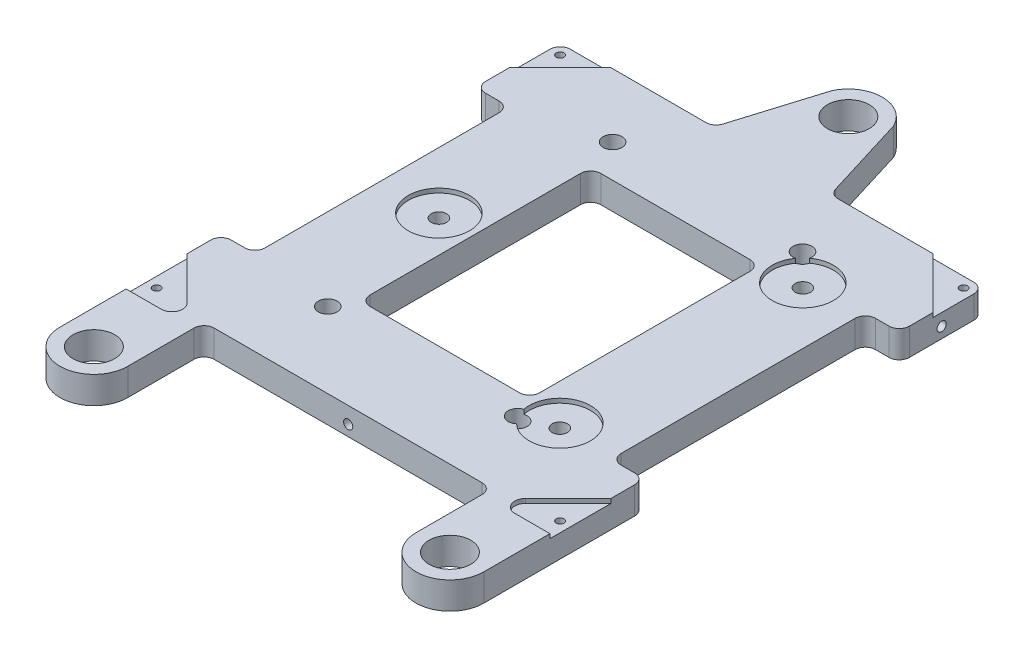
SolidWorks part; units mm, degrees
material "Invar"
ref_plane "Front" through (0, 0, 0) normal (0, 0, 1) x (1, 0, 0)
ref_plane "Top" through (0, 0, 0) normal (0, 1, 0) x (1, 0, 0)
ref_plane "Right" through (0, 0, 0) normal (1, 0, 0) x (0, 0, -1)
sketch "Sketch1" plane through (0, 0, 0) normal (0, 1, 0) x (1, 0, 0)
  line L0 (62.5, -85) -> (9.0874, 89.1737) construction
  line L1 (62.5, -62.5) -> (-62.5, -62.5)
  line L2 (62.5, -62.5) -> (62.5, 62.5)
  line L3 (62.5, 62.5) -> (-62.5, 62.5)
  line L4 (-62.5, -62.5) -> (-62.5, 62.5)
  line L5 (62.5, -62.5) -> (-62.5, 62.5) construction
  line L6 (62.5, 62.5) -> (-62.5, -62.5) construction
  line L7 (-10, 62.5) -> (10, 62.5)
  line L8 (-10, 62.5) -> (-10, 85)
  line L9 (-10, 85) -> (10, 85)
  line L10 (10, 62.5) -> (10, 85)
  line L11 (-62.5, -62.5) -> (-42.5, -62.5)
  line L12 (-62.5, -62.5) -> (-62.5, -85)
  line L13 (-62.5, -85) -> (-42.5, -85)
  line L14 (-42.5, -62.5) -> (-42.5, -85)
  line L15 (62.5, -62.5) -> (42.5, -62.5)
  line L16 (62.5, -62.5) -> (62.5, -85)
  line L17 (62.5, -85) -> (42.5, -85)
  line L18 (42.5, -62.5) -> (42.5, -85)
  line L19 (-62.5, -85) -> (-9.0874, 89.1737) construction
  line L20 (-62.5, 25.4) -> (-62.5, -25.4)
  line L21 (-9.0874, 89.1737) -> (-17.2672, 62.5)
  line L22 (9.0874, 89.1737) -> (17.2672, 62.5)
  line L24 (62.5, 25.4) -> (62.5, -25.4)
  arc A0 (-62.5, -85) -> (-42.5, -85) centre (-52.5, -85) ccw
  arc A1 (42.5, -85) -> (62.5, -85) centre (52.5, -85) ccw
  arc A2 (-10, 85) -> (10, 85) centre (0, 85) cw
  point P0 (0, 0)
  point P22 (0, 62.5)
  dimension "D1" = 10
  dimension "D2" = 170
  dimension "D3" = 125
  dimension "D4" = 125
extrude "Boss-Extrude1" add sketch "Sketch1" against normal blind 8 contours L4 L1 L2 L3 | L14 L1 L12 L13 | L13 A0 | L17 A1 | L1 L18 L17 L16 | A2 L9 | L3 L10 L9 L8 | L22 A2 L10 L3 | L8 A2 L21 L3
sketch "Sketch8" plane through (0, 0, 0) normal (0, 1, 0) x (1, 0, 0)
  line L0 (-62.5, -85) -> (-62.5, 62.5) construction
  line L1 (25, -34) -> (-25, -34)
  line L2 (25, -34) -> (25, 34)
  line L3 (25, 34) -> (-25, 34)
  line L4 (-25, -34) -> (-25, 34)
  line L5 (25, -34) -> (-25, 34) construction
  line L6 (25, 34) -> (-25, -34) construction
  line L7 (-62.5, 37.5) -> (-52.5, 37.5)
  line L8 (-62.5, 37.5) -> (-62.5, -37.5)
  line L9 (-62.5, -37.5) -> (-52.5, -37.5)
  line L10 (-52.5, 37.5) -> (-52.5, -37.5)
  line L11 (62.5, -85) -> (62.5, 62.5) construction
  line L12 (62.5, 37.5) -> (52.5, 37.5)
  line L13 (62.5, 37.5) -> (62.5, -37.5)
  line L14 (62.5, -37.5) -> (52.5, -37.5)
  line L15 (52.5, 37.5) -> (52.5, -37.5)
  point P0 (0, 0)
  point P18 (-52.5, 0)
  dimension "D1" = 68
  dimension "D2" = 50
  dimension "D3" = 10
  dimension "D4" = 75
extrude "Cut-Extrude2" cut sketch "Sketch8" against normal through all
hole_wizard "9/16-12 Tapped Hole1" positions "3DSketch1" profile "Sketch3" tap size "9/16-12" standard "ANSI Inch" end condition through all
sketch3d "3DSketch1"
  line L0 (-52.5, -8, 85) -> (-52.5, 0, 85) construction
  line L1 (0, -8, -85) -> (0, 0, -85) construction
  line L2 (52.5, -8, 85) -> (52.5, 0, 85) construction
  point P0 (-52.5, 0, 85)
  point P4 (0, 0, -85)
  point P8 (52.5, 0, 85)
sketch "Sketch3" plane through (-52.5, 0, 85) normal (1, 0, 0) x (0, 0, 1)
  line L0 (0, 0) -> (0, 8)
  line L1 (0, 8) -> (6.1519, 8)
  line L2 (6.1519, 8) -> (6.1519, 0)
  line L5 (6.1519, 0) -> (0, 0)
  line L11 (0, -6.35) -> (0, 107.95) construction
  dimension "Thru Tap Drill Dia." = 12.3038
  dimension "Thru Tap Drill Depth" = 8
cosmetic thread "Hole Thread1" parameters "D2"=14.2875
cosmetic thread "Hole Thread2" parameters "D2"=14.2875
cosmetic thread "Hole Thread3" parameters "D2"=14.2875
fillet "Fillet1" radius 3 18 edges at (17.2672, -4, -62.5) (62.5, -4, -62.5) (42.5, -4, 62.5) (-42.5, -4, 62.5) (-62.5, -4, -62.5) (-17.2672, -4, -62.5) (-25, -4, 34) (-25, -4, -34) (25, -4, -34) (25, -4, 34) (-62.5, -4, 37.5) (-62.5, -4, -37.5) (-52.5, -4, -37.5) (-52.5, -4, 37.5) (62.5, -4, -37.5) (62.5, -4, 37.5) (52.5, -4, 37.5) (52.5, -4, -37.5)
hole_wizard "M4 Clearance Hole1" positions "Sketch5" profile "Sketch4" hole size "M4" standard "ANSI Metric" end condition through all
sketch "Sketch5" plane through (0, 0, 0) normal (0, 1, 0) x (1, 0, 0)
  point P0 (-35.745, 0)
  point P2 (35.745, -35.829)
  point P4 (35.745, 35.829)
sketch "Sketch4" plane through (-35.745, 0, 0) normal (1, 0, 0) x (0, 0, 1)
  line L0 (0, 0) -> (0, 8)
  line L1 (0, 8) -> (2.25, 8)
  line L2 (2.25, 8) -> (2.25, 0)
  line L5 (2.25, 0) -> (0, 0)
  line L11 (0, -6.35) -> (0, 107.95) construction
  dimension "Thru Hole Dia." = 4.5
  dimension "Thru Hole Depth" = 8
sketch "Sketch7" plane through (0, 0, 0) normal (0, 1, 0) x (1, 0, 0)
  circle A0 centre (-35.745, 0) radius 9.0297
  circle A1 centre (35.745, 35.829) radius 9.0297
  circle A2 centre (35.745, -35.829) radius 9.0297
extrude "Cut-Extrude1" cut sketch "Sketch7" against normal blind 1.27
hole_wizard "#4-40 Tapped Hole1" positions "Sketch10" profile "Sketch9" tap size "#4-40" standard "ANSI Inch" end condition through all
sketch "Sketch10" plane through (0, 0, 0) normal (0, 1, 0) x (1, 0, 0)
  line L35 (-62.5, 59.5) -> (-62.5, 40.5)
  line L36 (-59.5, 37.5) -> (-55.5, 37.5)
  line L37 (-52.5, 34.5) -> (-52.5, -34.5)
  line L38 (-55.5, -37.5) -> (-59.5, -37.5)
  line L39 (-62.5, -40.5) -> (-62.5, -85)
  line L40 (-42.5, -85) -> (-42.5, -65.5)
  line L41 (-39.5, -62.5) -> (39.5, -62.5)
  line L42 (42.5, -65.5) -> (42.5, -85)
  line L43 (62.5, -85) -> (62.5, -40.5)
  line L44 (59.5, -37.5) -> (55.5, -37.5)
  line L45 (52.5, -34.5) -> (52.5, 34.5)
  line L46 (55.5, 37.5) -> (59.5, 37.5)
  line L47 (62.5, 40.5) -> (62.5, 59.5)
  line L48 (59.5, 62.5) -> (19.4851, 62.5)
  line L51 (-19.4851, 62.5) -> (-59.5, 62.5)
  line L52 (-62.5, 59.5) -> (-62.5, 40.5)
  line L53 (-59.5, 37.5) -> (-55.5, 37.5)
  line L54 (-52.5, 34.5) -> (-52.5, -34.5)
  line L55 (-55.5, -37.5) -> (-59.5, -37.5)
  line L56 (-62.5, -40.5) -> (-62.5, -85)
  line L57 (-42.5, -85) -> (-42.5, -65.5)
  line L58 (-39.5, -62.5) -> (39.5, -62.5)
  line L59 (42.5, -65.5) -> (42.5, -85)
  line L60 (62.5, -85) -> (62.5, -40.5)
  line L61 (59.5, -37.5) -> (55.5, -37.5)
  line L62 (52.5, -34.5) -> (52.5, 34.5)
  line L63 (55.5, 37.5) -> (59.5, 37.5)
  line L64 (62.5, 40.5) -> (62.5, 59.5)
  line L65 (59.5, 62.5) -> (19.4851, 62.5)
  line L68 (-19.4851, 62.5) -> (-59.5, 62.5)
  line L105 (16.6169, 64.6204) -> (9.0874, 89.1737)
  line L106 (16.6169, 64.6204) -> (9.0874, 89.1737)
  line L107 (-9.0874, 89.1737) -> (-16.6169, 64.6204)
  line L108 (-9.0874, 89.1737) -> (-16.6169, 64.6204)
  arc A34 (-62.5, 40.5) -> (-59.5, 37.5) centre (-59.5, 40.5) ccw
  arc A35 (-52.5, 34.5) -> (-55.5, 37.5) centre (-55.5, 34.5) ccw
  arc A36 (-55.5, -37.5) -> (-52.5, -34.5) centre (-55.5, -34.5) ccw
  arc A37 (-59.5, -37.5) -> (-62.5, -40.5) centre (-59.5, -40.5) ccw
  arc A38 (-62.5, -85) -> (-42.5, -85) centre (-52.5, -85) ccw
  arc A39 (-39.5, -62.5) -> (-42.5, -65.5) centre (-39.5, -65.5) ccw
  arc A40 (42.5, -65.5) -> (39.5, -62.5) centre (39.5, -65.5) ccw
  arc A41 (42.5, -85) -> (62.5, -85) centre (52.5, -85) ccw
  arc A42 (62.5, -40.5) -> (59.5, -37.5) centre (59.5, -40.5) ccw
  arc A43 (52.5, -34.5) -> (55.5, -37.5) centre (55.5, -34.5) ccw
  arc A44 (55.5, 37.5) -> (52.5, 34.5) centre (55.5, 34.5) ccw
  arc A45 (59.5, 37.5) -> (62.5, 40.5) centre (59.5, 40.5) ccw
  arc A46 (62.5, 59.5) -> (59.5, 62.5) centre (59.5, 59.5) ccw
  arc A48 (9.0874, 89.1737) -> (-9.0874, 89.1737) centre (0, 85) ccw
  arc A50 (-59.5, 62.5) -> (-62.5, 59.5) centre (-59.5, 59.5) ccw
  arc A51 (-62.5, 40.5) -> (-59.5, 37.5) centre (-59.5, 40.5) ccw
  arc A52 (-52.5, 34.5) -> (-55.5, 37.5) centre (-55.5, 34.5) ccw
  arc A53 (-55.5, -37.5) -> (-52.5, -34.5) centre (-55.5, -34.5) ccw
  arc A54 (-59.5, -37.5) -> (-62.5, -40.5) centre (-59.5, -40.5) ccw
  arc A55 (-62.5, -85) -> (-42.5, -85) centre (-52.5, -85) ccw
  arc A56 (-39.5, -62.5) -> (-42.5, -65.5) centre (-39.5, -65.5) ccw
  arc A57 (42.5, -65.5) -> (39.5, -62.5) centre (39.5, -65.5) ccw
  arc A58 (42.5, -85) -> (62.5, -85) centre (52.5, -85) ccw
  arc A59 (62.5, -40.5) -> (59.5, -37.5) centre (59.5, -40.5) ccw
  arc A60 (52.5, -34.5) -> (55.5, -37.5) centre (55.5, -34.5) ccw
  arc A61 (55.5, 37.5) -> (52.5, 34.5) centre (55.5, 34.5) ccw
  arc A62 (59.5, 37.5) -> (62.5, 40.5) centre (59.5, 40.5) ccw
  arc A63 (62.5, 59.5) -> (59.5, 62.5) centre (59.5, 59.5) ccw
  arc A65 (9.0874, 89.1737) -> (-9.0874, 89.1737) centre (0, 85) ccw
  arc A67 (-59.5, 62.5) -> (-62.5, 59.5) centre (-59.5, 59.5) ccw
  arc A140 (16.6169, 64.6204) -> (19.4851, 62.5) centre (19.4851, 65.5) ccw
  arc A141 (16.6169, 64.6204) -> (19.4851, 62.5) centre (19.4851, 65.5) ccw
  arc A142 (-19.4851, 62.5) -> (-16.6169, 64.6204) centre (-19.4851, 65.5) ccw
  arc A143 (-19.4851, 62.5) -> (-16.6169, 64.6204) centre (-19.4851, 65.5) ccw
  point P0 (-59.5, 59.5)
  point P283 (59.5, 59.5)
  point P284 (59.5, -59.5)
  point P285 (-59.5, -59.5)
  dimension "D2" = 125
  dimension "D3" = 3
  dimension "D4" = 3
  dimension "D1" = 0
  dimension "D5" = 2
  dimension "D6" = 2
sketch "Sketch9" plane through (-59.5, 0, -59.5) normal (1, 0, 0) x (0, 0, 1)
  line L0 (0, 0) -> (0, 8)
  line L1 (0, 8) -> (1.1303, 8)
  line L2 (1.1303, 8) -> (1.1303, 0)
  line L5 (1.1303, 0) -> (0, 0)
  line L11 (0, -6.35) -> (0, 107.95) construction
  dimension "Thru Tap Drill Dia." = 2.2606
  dimension "Thru Tap Drill Depth" = 8
cosmetic thread "Hole Thread4" parameters "D2"=2.8448
cosmetic thread "Hole Thread5" parameters "D2"=2.8448
cosmetic thread "Hole Thread6" parameters "D2"=2.8448
cosmetic thread "Hole Thread7" parameters "D2"=2.8448
sketch "Sketch11" plane through (0, 0, 0) normal (0, 1, 0) x (1, 0, 0)
  line L0 (-62.5, 47.5) -> (-47.5, 62.5)
  line L1 (-62.5, 40.5) -> (-62.5, 59.5) construction
  line L2 (-19.4851, 62.5) -> (-59.5, 62.5) construction
  line L3 (-62.5, -47.5) -> (-44.5, -65.5)
  line L4 (-62.5, -85) -> (-62.5, -40.5) construction
  line L5 (-44.5, -65.5) -> (-62.5, -65.5)
  line L6 (-62.5, -65.5) -> (-62.5, -47.5)
  line L7 (-62.5, 47.5) -> (-62.5, 59.5)
  line L8 (-47.5, 62.5) -> (-59.5, 62.5)
  line L9 (39.5, -62.5) -> (-39.5, -62.5) construction
  arc A0 (-59.5, 62.5) -> (-62.5, 59.5) centre (-59.5, 59.5) ccw construction
  arc A1 (-59.5, 62.5) -> (-62.5, 59.5) centre (-59.5, 59.5) ccw
  dimension "D1" = 15
  dimension "D2" = 15
  dimension "D3" = 15
  dimension "D4" = 135
  dimension "D5" = 3
extrude "Cut-Extrude3" cut sketch "Sketch11" against normal blind 1.27
fillet "Fillet2" radius 3.175 1 edges at (-44.5, -0.635, 65.5)
mirror "Mirror1" about plane through (0, 0, 0) normal (1, 0, 0) of "Cut-Extrude3", "Fillet2"
hole_wizard "#6-32 Tapped Hole1" positions "Sketch12" profile "Sketch13" tap size "#6-32" standard "ANSI Inch"
sketch "Sketch12" plane through (62.5, 0, 0) normal (1, 0, 0) x (0, 0, -1)
  line L0 (40.5, 0) -> (40.5, -8) construction
  line L1 (40.5, -8) -> (59.5, -8) construction
  point P0 (50.025, -4.825)
  dimension "D1" = 9.525
  dimension "D2" = 3.175
sketch "Sketch13" plane through (62.5, -4.825, -50.025) normal (0, 1, 0) x (0, 0, -1)
  line L0 (0, 0) -> (0, 11.7827)
  line L1 (0, 11.7827) -> (1.3525, 10.97)
  line L2 (1.3525, 10.97) -> (1.3525, 0)
  line L5 (1.3525, 0) -> (0, 0)
  line L10 (0, 11.7827) -> (-1.3525, 10.97) construction
  line L11 (0, -6.35) -> (0, 107.95) construction
  dimension "Tap Drill Dia." = 2.7051
  dimension "Tap Drill Depth" = 10.97
  dimension "Drill Angle" = 118
cosmetic thread "Hole Thread9" parameters "D1"=7.01, "D2"=3.5052
mirror "Mirror2" about plane through (0, 0, 0) normal (1, 0, 0) of "#6-32 Tapped Hole1"
hole_wizard "CBORE for #4 Socket Head Cap Screw1" positions "Sketch14" profile "Sketch15" counterbore size "#4" standard "ANSI Inch" end condition through all
sketch "Sketch14" plane through (0, 0, 0) normal (0, 1, 0) x (1, 0, 0)
  line L0 (0, 34) -> (0, -34) construction
  line L1 (22, 34) -> (-22, 34) construction
  line L2 (-22, -34) -> (22, -34) construction
  line L4 (-25, 0) -> (25, 0) construction
  line L5 (-25, 31) -> (-25, -31) construction
  line L6 (25, -31) -> (25, 31) construction
  point P0 (-28.276, 43.752)
  point P22 (27.724, 43.752)
  point P23 (27.724, -40.248)
  point P24 (-28.276, -40.248)
  dimension "D1" = 28.276
  dimension "D2" = 43.752
  dimension "D3" = 2
  dimension "D4" = 2
sketch "Sketch15" plane through (-28.276, 0, -43.752) normal (1, 0, 0) x (0, 0, 1)
  line L0 (0, 0) -> (0, 8)
  line L1 (0, 8) -> (1.6319, 8)
  line L3 (1.6319, 8) -> (1.6319, 6)
  line L4 (1.6319, 6) -> (2.7788, 6)
  line L5 (2.7788, 6) -> (2.7788, 0)
  line L7 (2.7788, 0) -> (0, 0)
  line L11 (0, -6.35) -> (0, 107.95) construction
  dimension "Thru Hole Dia." = 3.2639
  dimension "Thru Hole Depth" = 8
  dimension "C'Bore Dia." = 5.5575
  dimension "C'Bore Depth" = 6
hole_wizard "#6-32 Tapped Hole2" positions "Sketch16" profile "Sketch17" tap size "#6-32" standard "ANSI Inch"
sketch "Sketch16" plane through (0, 0, 62.5) normal (0, 0, 1) x (1, 0, 0)
  line L0 (0, -8) -> (0, 0) construction
  line L1 (39.5, -8) -> (-39.5, -8) construction
  line L2 (39.5, 0) -> (-39.5, 0) construction
  point P0 (0, -4.825)
  dimension "D1" = 3.175
sketch "Sketch17" plane through (0, -4.825, 62.5) normal (1, 0, 0) x (0, -1, 0)
  line L0 (0, 0) -> (0, 11.7827)
  line L1 (0, 11.7827) -> (1.3525, 10.97)
  line L2 (1.3525, 10.97) -> (1.3525, 0)
  line L5 (1.3525, 0) -> (0, 0)
  line L10 (0, 11.7827) -> (-1.3525, 10.97) construction
  line L11 (0, -6.35) -> (0, 107.95) construction
  dimension "Tap Drill Dia." = 2.7051
  dimension "Tap Drill Depth" = 10.97
  dimension "Drill Angle" = 118
cosmetic thread "Hole Thread10" parameters "D1"=7.01, "D2"=3.5052
equation "\"D1@Sketch7\"=25.4*.711"
equation "\"D2@Sketch5\"=\"D1@Sketch5\""
